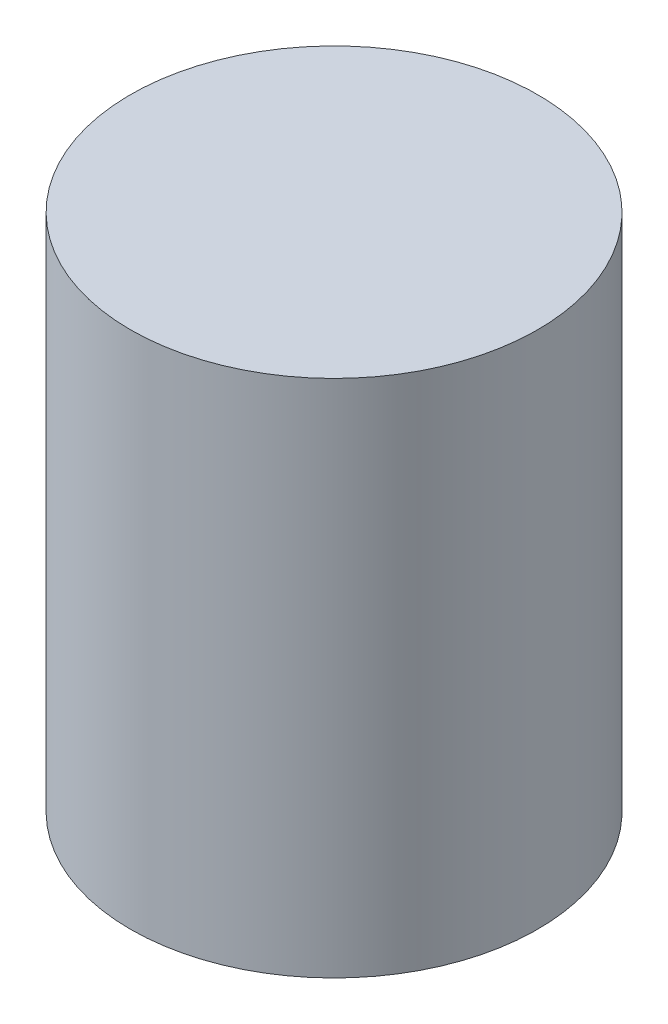
SolidWorks part; units mm, degrees
ref_plane "Front Plane" through (0, 0, 0) normal (0, 0, 1) x (1, 0, 0)
ref_plane "Top Plane" through (0, 0, 0) normal (0, 1, 0) x (1, 0, 0)
ref_plane "Right Plane" through (0, 0, 0) normal (1, 0, 0) x (0, 0, -1)
sketch "Sketch1" plane through (0, 0, 0) normal (0, 1, 0) x (1, 0, 0)
  circle A0 centre (-22.7706, 24.3231) radius 11
extrude "Boss-Extrude2" add sketch "Sketch1" along normal blind 28.05
